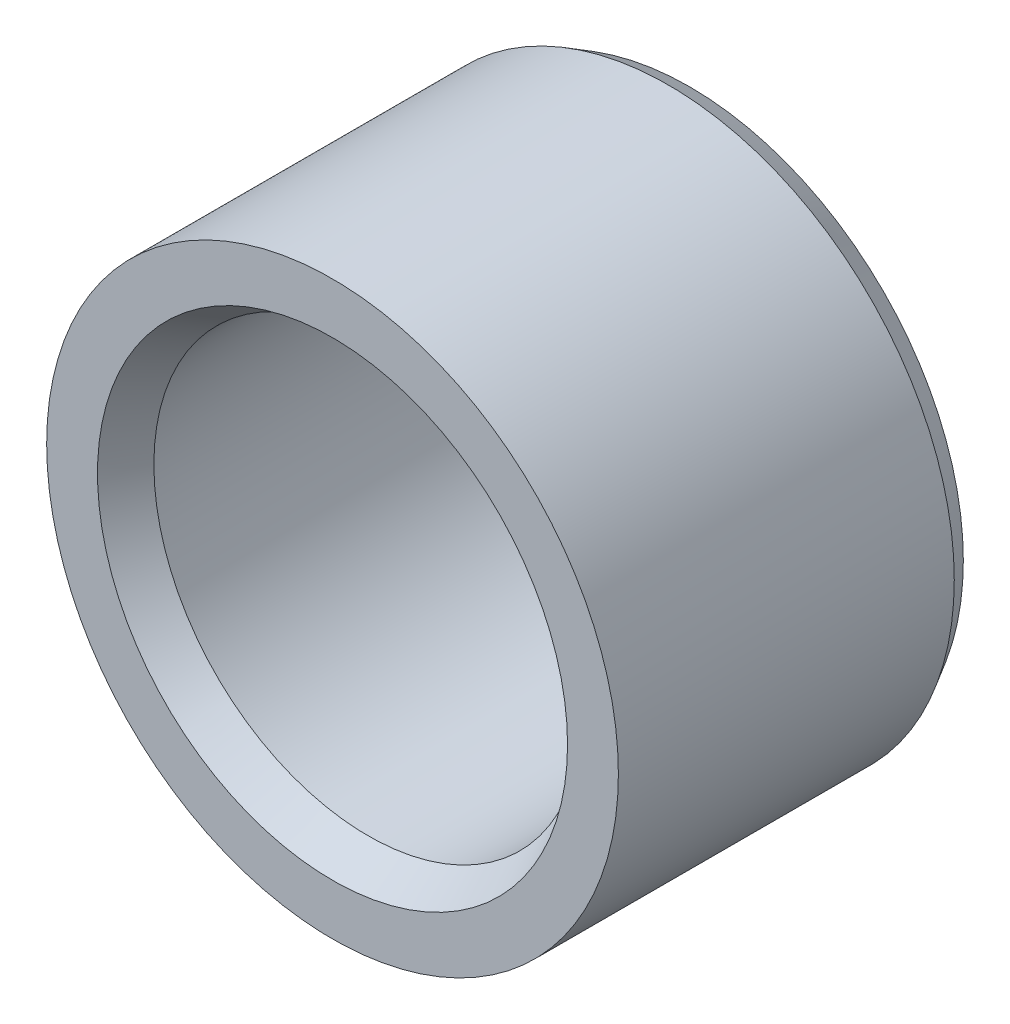
SolidWorks part; units mm, degrees
ref_plane "Front Plane" through (0, 0, 0) normal (0, 0, 1) x (1, 0, 0)
ref_plane "Top Plane" through (0, 0, 0) normal (0, 1, 0) x (1, 0, 0)
ref_plane "Right Plane" through (0, 0, 0) normal (1, 0, 0) x (0, 0, -1)
sketch "Sketch1" plane through (0, 0, 0) normal (0, 0, 1) x (1, 0, 0)
  circle A0 centre (0, 0) radius 4
  circle A1 centre (0, 0) radius 3
  dimension "D1" = 6
  dimension "D2" = 8
extrude "Boss-Extrude1" add sketch "Sketch1" along normal blind 5
chamfer "Chamfer1" distance 0.3 angle 30 1 edges at (4, 0, 0)
chamfer "Chamfer2" distance 0.5 angle 30 1 edges at (3, 0, 5)
